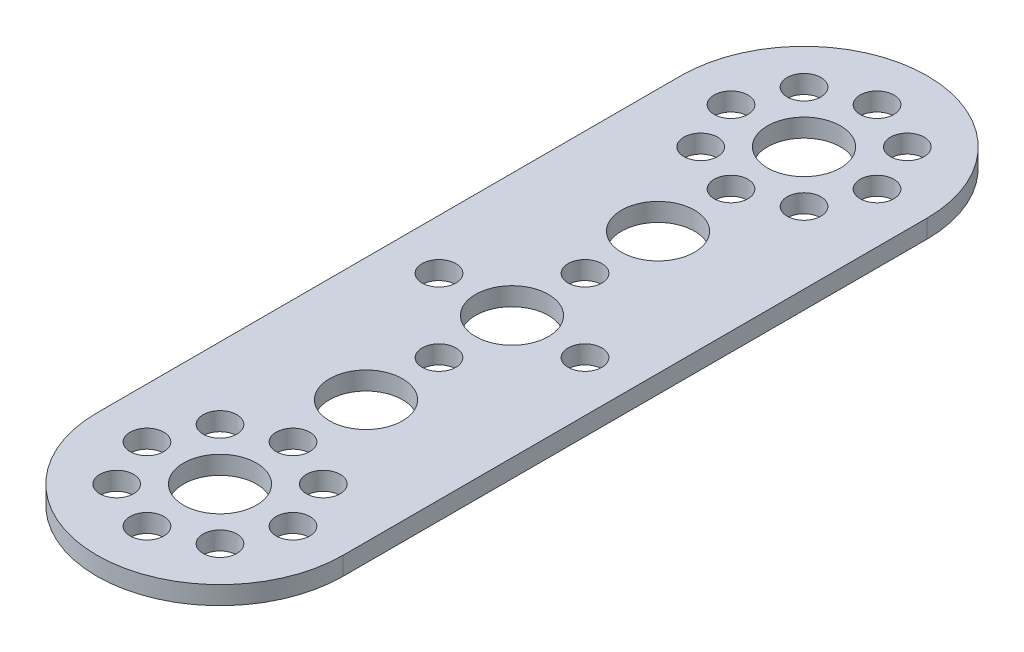
SolidWorks part; units mm, degrees
material "5052-H32"
ref_plane "Front Plane" through (0, 0, 0) normal (0, 0, 1) x (1, 0, 0)
ref_plane "Top Plane" through (0, 0, 0) normal (0, 1, 0) x (1, 0, 0)
ref_plane "Right Plane" through (0, 0, 0) normal (1, 0, 0) x (0, 0, -1)
sketch "Sketch2" plane through (0, 0, 0) normal (0, 1, 0) x (1, 0, 0)
  line L2 (-13.5, -32) -> (-13.5, 32)
  line L4 (13.5, -32) -> (13.5, 32)
  line L5 (-13.5, -48) -> (13.5, 48) construction
  line L6 (-13.5, 48) -> (13.5, -48) construction
  arc A0 (13.5, 32) -> (-13.5, 32) centre (0, 32) ccw
  arc A1 (-13.5, -32) -> (13.5, -32) centre (0, -32) ccw
  point P0 (0, 0)
  dimension "D1" = 27
  dimension "D2" = 32
  dimension "D3" = 32
extrude "Extrude1" add sketch "Sketch2" along normal blind 2
sketch "Sketch3" plane through (0, 2, 0) normal (0, 1, 0) x (1, 0, 0)
  circle B0 centre (0, -16) radius 4
  circle B1 centre (0, 16) radius 4
  circle B2 centre (0, 0) radius 4
  circle B3 centre (0, 8) radius 1.85
  circle B4 centre (0, -8) radius 1.85
  circle B5 centre (8, 0) radius 1.85
  circle B6 centre (-8, 0) radius 1.85
  circle B7 centre (0, -24) radius 1.85
  circle B8 centre (8, -32) radius 1.85
  circle B9 centre (0, -32) radius 4
  circle B10 centre (-8, -32) radius 1.85
  circle B11 centre (-5.66, -37.66) radius 1.85
  circle B12 centre (5.66, -37.66) radius 1.85
  circle B13 centre (0, -40) radius 1.85
  circle B14 centre (-5.66, -26.34) radius 1.85
  circle B15 centre (5.66, -26.34) radius 1.85
  circle B16 centre (0, 40) radius 1.85
  circle B17 centre (8, 32) radius 1.85
  circle B18 centre (0, 32) radius 4
  circle B19 centre (-8, 32) radius 1.85
  circle B20 centre (-5.66, 26.34) radius 1.85
  circle B21 centre (5.66, 26.34) radius 1.85
  circle B22 centre (0, 24) radius 1.85
  circle B23 centre (-5.66, 37.66) radius 1.85
  circle B24 centre (5.66, 37.66) radius 1.85
sketch_block_instance "TETRIX 96 Pattern-1"
sketch_block "TETRIX 96 Pattern" parameters "D1"=16, "D2"=16, "D3"=16, "D4"=16
extrude "Extrude2" cut sketch "Sketch3" against normal blind 2
